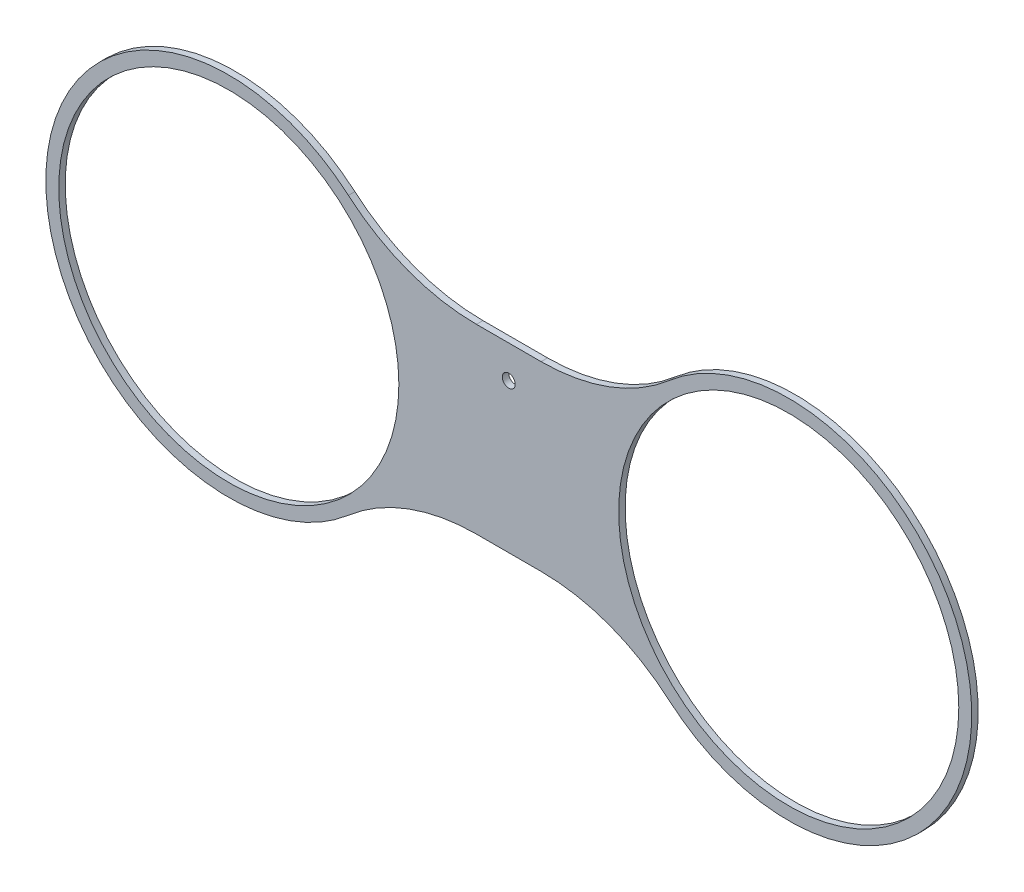
SolidWorks part; units mm, degrees
ref_plane "Front Plane" through (0, 0, 0) normal (0, 0, 1) x (1, 0, 0)
ref_plane "Top Plane" through (0, 0, 0) normal (0, 1, 0) x (1, 0, 0)
ref_plane "Right Plane" through (0, 0, 0) normal (1, 0, 0) x (0, 0, -1)
sketch "Sketch1" plane through (0, 0, 0) normal (0, 0, 1) x (1, 0, 0)
  line L0 (137.419, 0) -> (-137.4211, 0) construction
  line L1 (-15.8547, -44.5943) -> (15.8526, -44.5943)
  line L2 (15.8526, 44.5943) -> (-15.8547, 44.5943)
  line L3 (-0.0011, 44.5943) -> (-0.0011, -44.5943) construction
  line L4 (-78.704, 67.9795) -> (78.7018, -67.9795) construction
  line L5 (-78.704, -67.9795) -> (78.7018, 67.9795) construction
  circle A0 centre (137.419, 0) radius 83.4771 construction
  circle A1 centre (-137.4211, 0) radius 83.4771 construction
  circle A2 centre (137.419, 0) radius 83.4771
  circle A3 centre (-137.4211, 0) radius 83.4771
  arc A4 (-78.704, -67.9795) -> (-78.704, 67.9795) centre (-137.4211, 0) cw
  arc A5 (78.7018, -67.9795) -> (78.7018, 67.9795) centre (137.419, 0) ccw
  arc A6 (-78.704, 67.9795) -> (-15.8547, 44.5943) centre (-15.8547, 140.7429) ccw
  arc A7 (78.7018, 67.9795) -> (15.8526, 44.5943) centre (15.8526, 140.7429) cw
  arc A8 (78.7018, -67.9795) -> (15.8526, -44.5943) centre (15.8526, -140.7429) ccw
  arc A9 (-78.704, -67.9795) -> (-15.8547, -44.5943) centre (-15.8547, -140.7429) cw
  circle A11 centre (0, 28.575) radius 3.175
  point P10 (0, 0)
  point P16 (-0.0011, 44.5943)
  point P19 (-0.0011, 0)
  point P25 (-0.0011, 0)
  dimension "D1" = 16.0193
  dimension "D2" = 6.35
  dimension "D4" = 6.35
  dimension "D5" = 89.1887
extrude "Boss-Extrude1" add sketch "Sketch1" along normal blind 3.175
